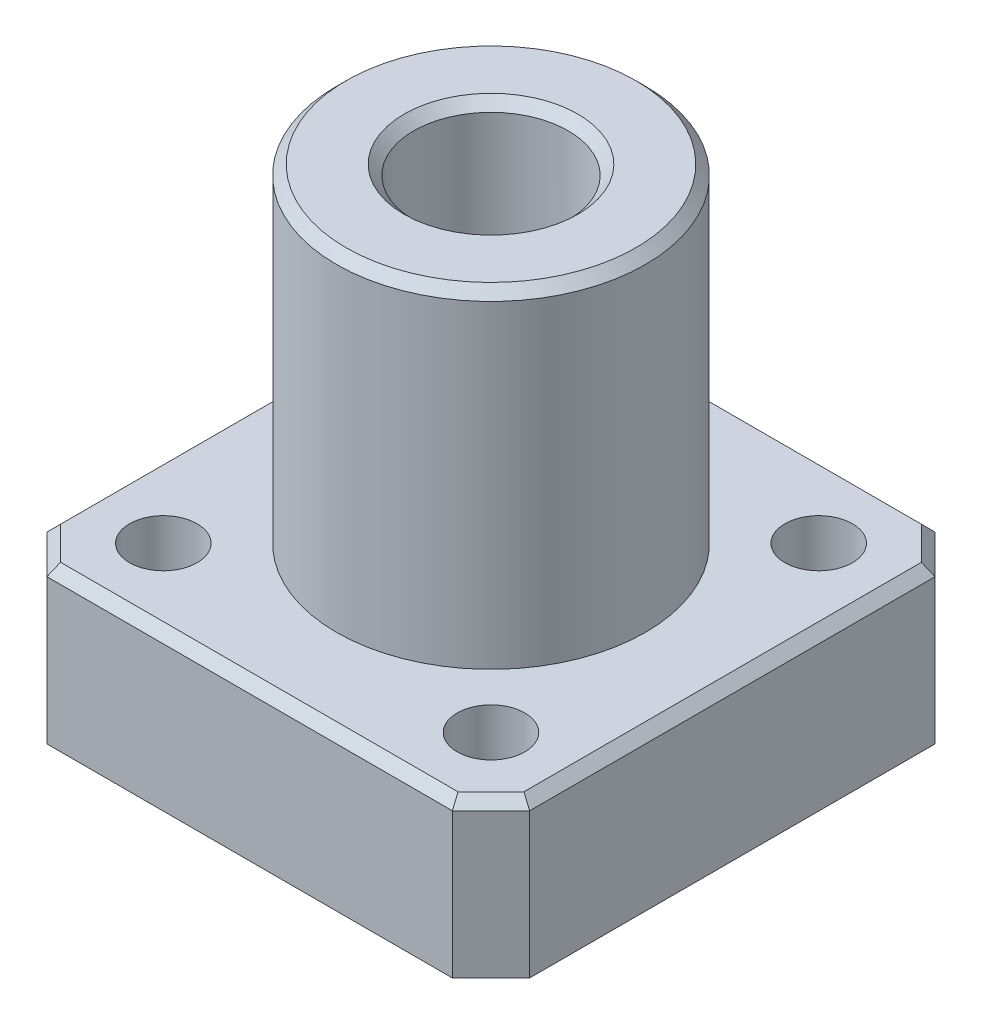
SolidWorks part; units mm, degrees
ref_plane "Face" through (0, 0, 0) normal (0, 0, 1) x (1, 0, 0)
ref_plane "Dessus" through (0, 0, 0) normal (0, 1, 0) x (1, 0, 0)
ref_plane "Droite" through (0, 0, 0) normal (1, 0, 0) x (0, 0, -1)
sketch "Esquisse1" plane through (0, 0, 0) normal (0, 1, 0) x (1, 0, 0)
  line L0 (0, 12.5) -> (25, 12.5) construction
  line L1 (0, 0) -> (25, 0)
  line L2 (0, 0) -> (0, 25)
  line L3 (0, 25) -> (25, 25)
  line L4 (25, 0) -> (25, 25)
  line L5 (12.5, 25) -> (12.5, 0) construction
  line L6 (0, 25) -> (25, 0) construction
  circle A0 centre (4.0147, 20.9853) radius 1.75
  circle A1 centre (20.9853, 20.9853) radius 1.75
  circle A2 centre (20.9853, 4.0147) radius 1.75
  circle A3 centre (4.0147, 4.0147) radius 1.75
  dimension "D2" = 3.5
  dimension "D1" = 25
  dimension "D3" = 24
extrude "Extrusion1" add sketch "Esquisse1" along normal blind 8
sketch "Esquisse2" plane through (0, 8, 0) normal (0, 1, 0) x (1, 0, 0)
  line L0 (0, 25) -> (25, 0) construction
  line L1 (0, 0) -> (25, 25) construction
  line L2 (25, 0) -> (25, 25) construction
  circle A0 centre (12.5, 12.5) radius 8
  dimension "D1" = 16
extrude "Extrusion2" add sketch "Esquisse2" along normal blind 17
chamfer "Chanfrein1" distance 2 angle 45 4 edges at (0, 4, -25) (25, 4, -25) (25, 4, 0) (0, 4, 0)
sketch "Esquisse3" plane through (0, 25, 0) normal (0, 1, 0) x (1, 0, 0)
  circle A0 centre (12.5, 12.5) radius 4
  dimension "D1" = 8
extrude "Extrusion3" cut sketch "Esquisse3" against normal up to next
chamfer "Chanfrein2" distance 0.5 angle 45 11 edges at (12.5, 0, -16.5) (24, 8, -24) (25, 8, -12.5) (24, 8, -1) (12.5, 8, 0) (1, 8, -1) (0, 8, -12.5) (1, 8, -24) (12.5, 8, -25) (12.5, 25, -4.5) (12.5, 25, -8.5)
